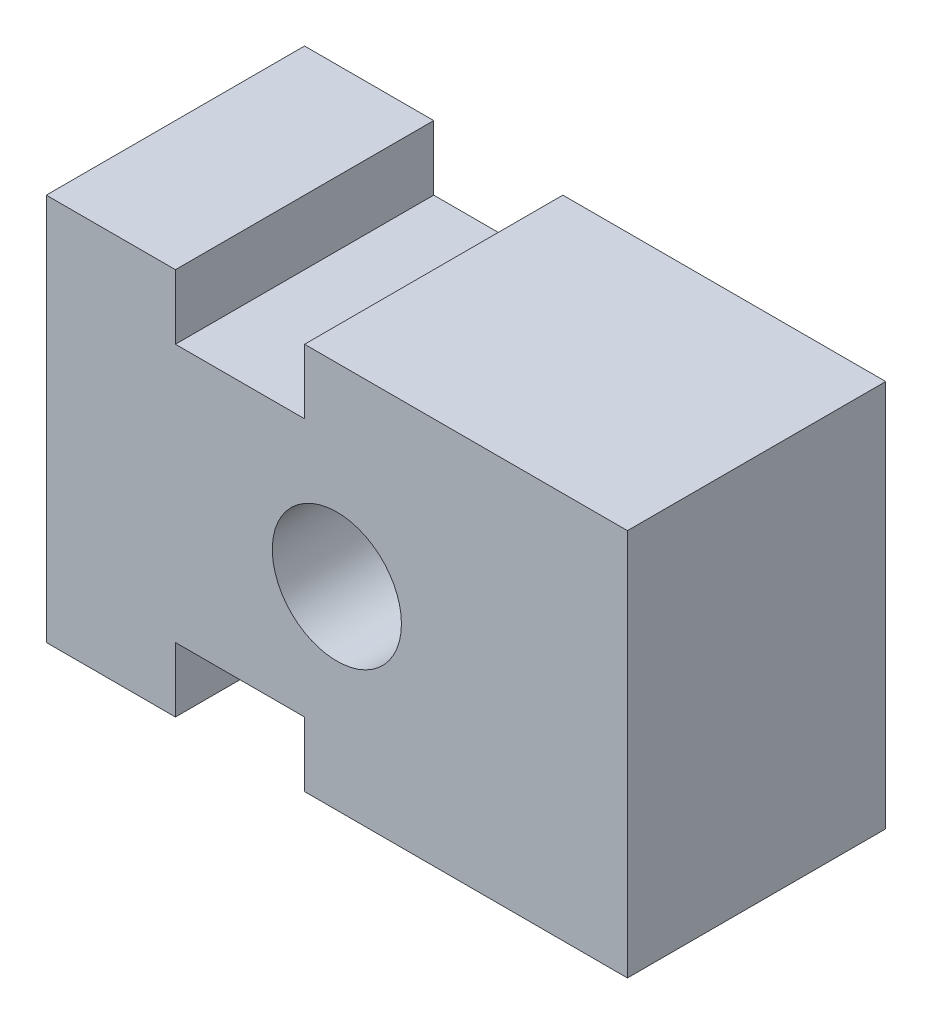
SolidWorks part; units mm, degrees
ref_plane "Front Plane" through (0, 0, 0) normal (0, 0, 1) x (1, 0, 0)
ref_plane "Top Plane" through (0, 0, 0) normal (0, 1, 0) x (1, 0, 0)
ref_plane "Right Plane" through (0, 0, 0) normal (1, 0, 0) x (0, 0, -1)
sketch "Sketch1" plane through (0, 0, 0) normal (0, 0, 1) x (1, 0, 0)
  line L12 (0, 76.2) -> (0, 0)
  line L13 (0, 0) -> (25.4, 0)
  line L14 (25.4, 0) -> (25.4, 12.7)
  line L15 (25.4, 12.7) -> (50.8, 12.7)
  line L16 (50.8, 12.7) -> (50.8, 0)
  line L17 (50.8, 0) -> (114.3, 0)
  line L18 (114.3, 0) -> (114.3, 76.2)
  line L19 (114.3, 76.2) -> (50.8, 76.2)
  line L20 (50.8, 76.2) -> (50.8, 63.5)
  line L21 (50.8, 63.5) -> (25.4, 63.5)
  line L22 (25.4, 63.5) -> (25.4, 76.2)
  line L23 (25.4, 76.2) -> (0, 76.2)
  point P3 (3.3493, 1.863)
  point P13 (0, 0)
  point P14 (0, 0)
  dimension "D1" = 50.8
  dimension "D2" = 76.2
  dimension "D3" = 114.3
  dimension "D4" = 25.4
  dimension "D5" = 63.5
  dimension "D6" = 12.7
extrude "Boss-Extrude1" add sketch "Sketch1" along normal blind 50.8
sketch "Sketch2" plane through (0, 0, 50.8) normal (0, 0, 1) x (1, 0, 0)
  line L0 (0, 76.2) -> (114.3, 0) construction
  line L1 (0, 0) -> (114.3, 76.2) construction
  circle A0 centre (57.15, 38.1) radius 12.7
  point P10 (57.15, 38.1)
  point P11 (0, 0)
extrude "Cut-Extrude1" cut sketch "Sketch2" against normal blind 50.8 contours A0
